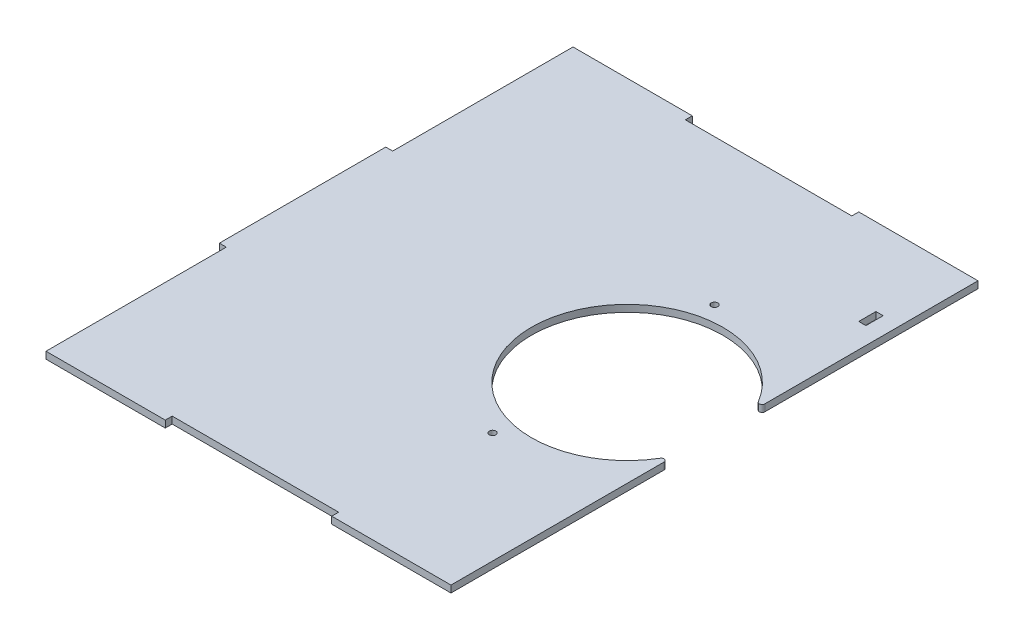
SolidWorks part; units mm, degrees
ref_plane "Front Plane" through (0, 0, 0) normal (0, 0, 1) x (1, 0, 0)
ref_plane "Top Plane" through (0, 0, 0) normal (0, 1, 0) x (1, 0, 0)
ref_plane "Right Plane" through (0, 0, 0) normal (1, 0, 0) x (0, 0, -1)
sketch "Sketch1" plane through (0, 0, 0) normal (0, 1, 0) x (1, 0, 0)
  line L1 (0, 0) -> (185.42, 0)
  line L2 (0, 0) -> (0, 241.3)
  line L3 (0, 241.3) -> (185.42, 241.3)
  line L4 (185.42, 0) -> (185.42, 241.3)
  dimension "D1" = 241.3
  dimension "D2" = 185.42
extrude "Boss-Extrude1" add sketch "Sketch1" along normal blind 3.175
sketch "Sketch2" plane through (0, 3.175, 0) normal (0, 1, 0) x (1, 0, 0)
  line L1 (189.23, 120.65) -> (185.42, 120.65) construction
  line L2 (185.42, 0) -> (185.42, 241.3) construction
  line L3 (101.6, 120.65) -> (0, 120.65) construction
  line L4 (0, 241.3) -> (0, 0) construction
  circle A4 centre (145.415, 120.65) radius 43.815
  dimension "D4" = 87.63
  dimension "D1" = 101.6
extrude "Cut-Extrude1" cut sketch "Sketch2" against normal through all
sketch "Sketch7" plane through (0, 3.175, 0) normal (0, 1, 0) x (1, 0, 0)
  line L0 (101.6, 120.65) -> (134.62, 120.65) construction
  arc A0 (185.42, 138.5205) -> (185.42, 102.7795) centre (145.415, 120.65) ccw construction
  circle B0 centre (134.62, 171.45) radius 1.5
  circle B1 centre (134.62, 69.85) radius 1.5
sketch_block_instance "Block-motorPlateHoles-1"
sketch_block "Block2" parameters "D1"=3
extrude "Cut-Extrude4" cut sketch "Sketch7" against normal through all
fillet "Fillet1" radius 1.27 2 edges at (185.42, 1.5875, -138.5205) (185.42, 1.5875, -102.7795)
sketch "Sketch8" plane through (0, 3.175, 0) normal (0, 1, 0) x (1, 0, 0)
  line L0 (92.71, 241.3) -> (92.71, 0) construction
  line L1 (54.61, 241.3) -> (130.81, 241.3)
  line L2 (54.61, 241.3) -> (54.61, 238.125)
  line L3 (54.61, 238.125) -> (130.81, 238.125)
  line L4 (130.81, 241.3) -> (130.81, 238.125)
  line L5 (54.61, 241.3) -> (130.81, 238.125) construction
  line L6 (54.61, 238.125) -> (130.81, 241.3) construction
  line L7 (0, 0) -> (185.42, 0) construction
  line L8 (185.42, 241.3) -> (0, 241.3) construction
  line L9 (92.71, 120.65) -> (0, 120.65) construction
  line L10 (0, 241.3) -> (0, 0) construction
  line L11 (54.61, 3.175) -> (130.81, 0) construction
  line L12 (54.61, 0) -> (130.81, 3.175) construction
  line L13 (130.81, 0) -> (130.81, 3.175)
  line L14 (54.61, 3.175) -> (130.81, 3.175)
  line L15 (54.61, 0) -> (54.61, 3.175)
  line L16 (54.61, 0) -> (130.81, 0)
  point P0 (92.71, 239.7125)
  point P19 (92.71, 1.5875)
  dimension "D1" = 76.2
  dimension "D2" = 3.175
extrude "Cut-Extrude5" cut sketch "Sketch8" against normal through all
sketch "Sketch11" plane through (0, 3.175, 0) normal (0, 1, 0) x (1, 0, 0)
  line L1 (-3.175, 158.75) -> (0, 158.75)
  line L2 (-3.175, 158.75) -> (-3.175, 82.55)
  line L3 (-3.175, 82.55) -> (0, 82.55)
  line L4 (0, 158.75) -> (0, 82.55)
  line L5 (-3.175, 158.75) -> (0, 82.55) construction
  line L6 (-3.175, 82.55) -> (0, 158.75) construction
  line L7 (54.61, 238.125) -> (130.81, 238.125) construction
  line L8 (54.61, 241.3) -> (54.61, 238.125) construction
  line L9 (0, 241.3) -> (0, 0) construction
  line L10 (-1.5875, 120.65) -> (101.6, 120.65) construction
  arc A0 (183.0589, 143.0708) -> (183.0589, 98.2292) centre (145.415, 120.65) ccw construction
  point P0 (-1.5875, 120.65)
extrude "Boss-Extrude3" add sketch "Sketch11" against normal up to surface (3.175 mm away) up to face at (110.5321, 0, -120.65)
sketch "Sketch12" plane through (0, 3.175, 0) normal (0, 1, 0) x (1, 0, 0)
  line L1 (174.244, 197.866) -> (177.546, 197.866)
  line L2 (174.244, 197.866) -> (174.244, 205.74)
  line L3 (174.244, 205.74) -> (177.546, 205.74)
  line L4 (177.546, 197.866) -> (177.546, 205.74)
  line L5 (185.42, 143.7207) -> (185.42, 241.3) construction
  line L7 (185.42, 241.3) -> (130.81, 241.3) construction
  dimension "D1" = 11.176
  dimension "D3" = 7.874
  dimension "D4" = 3.302
  dimension "D2" = 35.56
extrude "Cut-Extrude6" cut sketch "Sketch12" against normal through all
equation "\"flipWidth\"= 6.5"
equation "\"flipHeight\"= 4"
equation "\"spindleLength\"= 7.75"
equation "\"bearingID\"= 0.1559"
equation "\"motorWidth\"= 0.79"
equation "\"motorHeight\"= 1.0"
equation "\"motorLength\"= 1.58"
equation "\"spindleMaxDiam\"= 2.75"
equation "\"D4@Sketch2\"=\"spindleMaxDiam\" + 0.7"
equation "\"D1@Sketch1\"=\"height\""
equation "\"motorHoleID\"=0.119532"
equation "\"depth\"= 7.3"
equation "\"height\"= 9.5"
equation "\"bearingOD\"= 0.3539\t"
equation "\"totalLength\"= 15"
equation "\"D2@Sketch1\"=\"depth\""
equation "\"width\"= 8.60"
equation "\"stopperWidth\"= 0.13"
equation "\"stopperHeight\"= 0.31"
equation "\"stopperLength\"= 8.73"
equation "\"stopperLengthFromTop\"= 1.2 + 0.2"
equation "\"D3@Sketch12\"=\"stopperHeight\""
equation "\"D4@Sketch12\"=\"stopperWidth\""
equation "\"D2@Sketch12\"=\"stopperLengthFromTop\""
